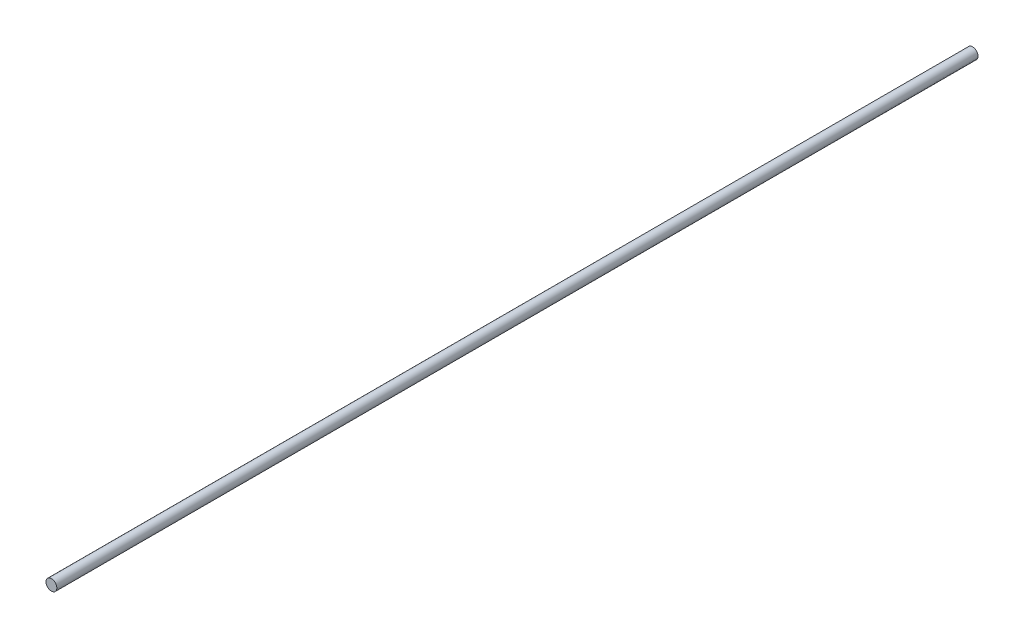
SolidWorks part; units mm, degrees
ref_plane "Plan de face" through (0, 0, 0) normal (0, 0, 1) x (1, 0, 0)
ref_plane "Plan de dessus" through (0, 0, 0) normal (0, 1, 0) x (1, 0, 0)
ref_plane "Plan de droite" through (0, 0, 0) normal (1, 0, 0) x (0, 0, -1)
sketch "Esquisse1" plane through (0, 0, 0) normal (0, 0, 1) x (1, 0, 0)
  circle A0 centre (0, 0) radius 4
  dimension "D1" = 8
extrude "Boss.-Extru.1" add sketch "Esquisse1" along normal blind 680
